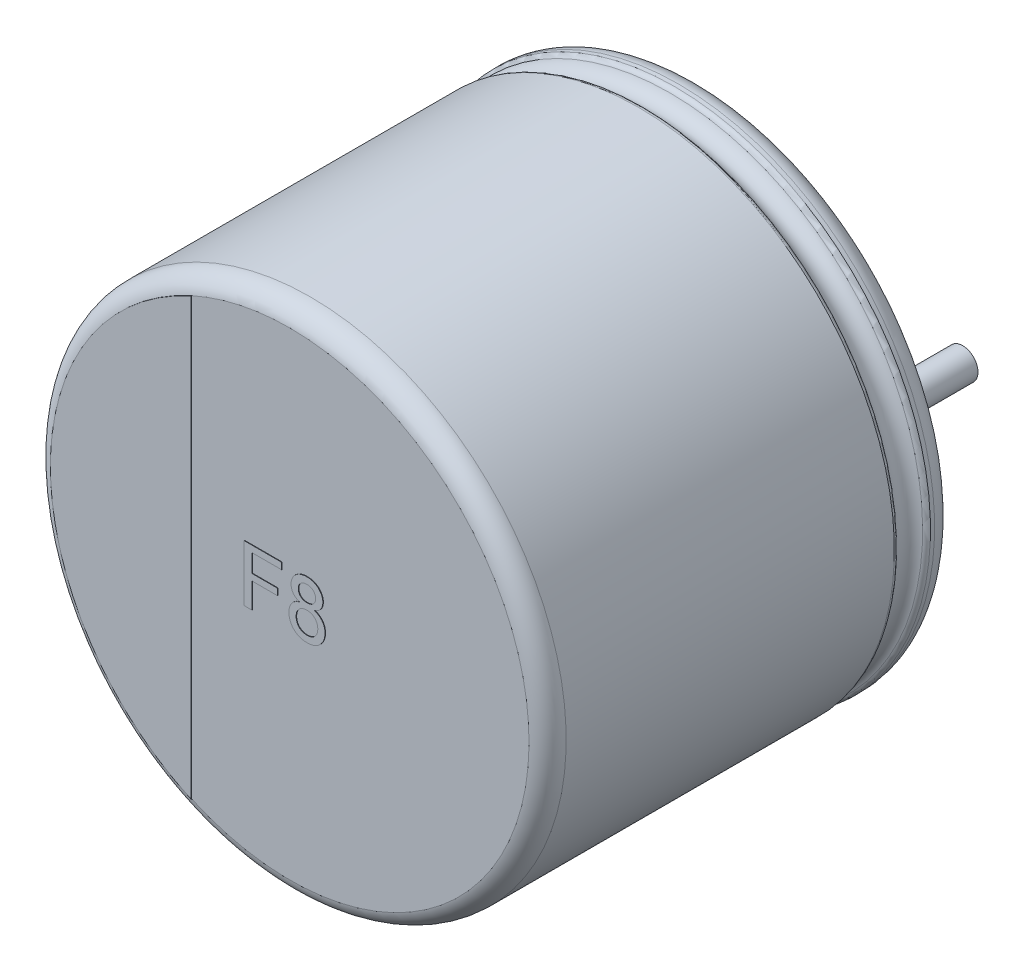
SolidWorks part; units mm, degrees
ref_plane "Plan de face" through (0, 0, 0) normal (0, 0, 1) x (1, 0, 0)
ref_plane "Plan de dessus" through (0, 0, 0) normal (0, 1, 0) x (1, 0, 0)
ref_plane "Plan de droite" through (0, 0, 0) normal (1, 0, 0) x (0, 0, -1)
sketch "Sketch10" plane through (0, 0, 0) normal (1, 0, 0) x (0, 0, -1)
  line L0 (18.1631, 0) -> (-18.9631, 0) construction
  line L1 (-8, 0) -> (-0.05, 0)
  line L2 (-8, 0) -> (-8, 4.6736)
  line L3 (-7.6, 5) -> (-1.1846, 5)
  line L4 (-0.05, 4.4031) -> (-0.05, 0)
  line L7 (-0.4794, 5) -> (-0.3982, 5)
  arc A0 (-8, 4.6736) -> (-7.6, 5) centre (-7.6068, 4.6001) cw
  arc A1 (-0.3982, 5) -> (-0.05, 4.4031) centre (-0.3982, 4.6) cw
  arc A2 (-0.5713, 4.9394) -> (-1.0926, 4.9394) centre (-0.832, 5.051) cw
  arc A3 (-1.0926, 4.9394) -> (-1.1846, 5) centre (-1.1846, 4.9) ccw
  arc A4 (-0.5713, 4.9394) -> (-0.4794, 5) centre (-0.4794, 4.9) cw
  point P4 (0.57, 0)
  point P13 (-8, 5)
  dimension "D2" = 0.4
  dimension "D3" = 0.4
  dimension "D4" = 0.1
  dimension "D5" = 0.1
  dimension "D1" = 5
revolve "Повернуть1" add sketch "Sketch10" angle 360 about L0
sketch "Эскиз2" plane through (0, 0, 0.05) normal (0, 0, -1) x (-1, 0, 0)
  line L1 (0, 0.7993) -> (0, -1.0496) construction
  line L2 (-2.5, 0) -> (2.3813, 0) construction
  circle A3 centre (-2.5, 0) radius 0.3
  circle A7 centre (2.5, 0) radius 0.3
  dimension "D1" = 5
extrude "Бобышка-Вытянуть1" add sketch "Эскиз2" along normal blind 2.7
sketch "Эскиз4" plane through (0, 0, 8) normal (0, 0, 1) x (1, 0, 0)
  line L0 (-1.9206, -4.2607) -> (-1.9206, 4.2607)
  circle A1 centre (0, 0) radius 4.6736 construction
  arc A2 (-1.9206, 4.2607) -> (-1.9206, -4.2607) centre (0, 0) ccw
extrude "Бобышка-Вытянуть2" add sketch "Эскиз4" along normal blind 0.01
sketch "Эскиз5" plane through (0, 0, 8) normal (0, 0, 1) x (1, 0, 0)
  text T0 "F8" font "Arial" height 1.1
extrude "Текст" add sketch "Эскиз5" along normal blind 0.01
sketch "Эскиз6" plane through (0, 0, 0.05) normal (0, 0, -1) x (-1, 0, 0)
  line L0 (-2.5, 0.6247) -> (-2.6072, 0.6247)
  line L1 (-2.5, -0.6247) -> (-2.6072, -0.6247)
  line L2 (2.5, -0.6247) -> (2.6072, -0.6247)
  line L3 (2.5, 0.6247) -> (2.6072, 0.6247)
  arc A0 (-2.8442, -0.9542) -> (2.8442, -0.9542) centre (0, 0) ccw
  arc A1 (-2.5, -0.6247) -> (-2.5, 0.6247) centre (-2.5, 0) ccw
  arc A2 (2.5, 0.6247) -> (2.5, -0.6247) centre (2.5, 0) ccw
  arc A3 (2.8442, 0.9542) -> (-2.8442, 0.9542) centre (0, 0) ccw
  arc A4 (2.6072, 0.6247) -> (2.8442, 0.9542) centre (2.6072, 0.8747) ccw
  arc A5 (2.6072, -0.6247) -> (2.8442, -0.9542) centre (2.6072, -0.8747) cw
  arc A6 (-2.8442, -0.9542) -> (-2.6072, -0.6247) centre (-2.6072, -0.8747) cw
  arc A7 (-2.6072, 0.6247) -> (-2.8442, 0.9542) centre (-2.6072, 0.8747) cw
  point P7 (2.9342, 0.6247)
  point P23 (0, -3)
  point P24 (0, 3)
  dimension "D1" = 0.25
  dimension "D2" = 6
extrude "Бобышка-Вытянуть5" add sketch "Эскиз6" along normal blind 0.05 contours A3 A7 L0 A1 L1 A6 A0 A5 L2 A2 L3 A4
